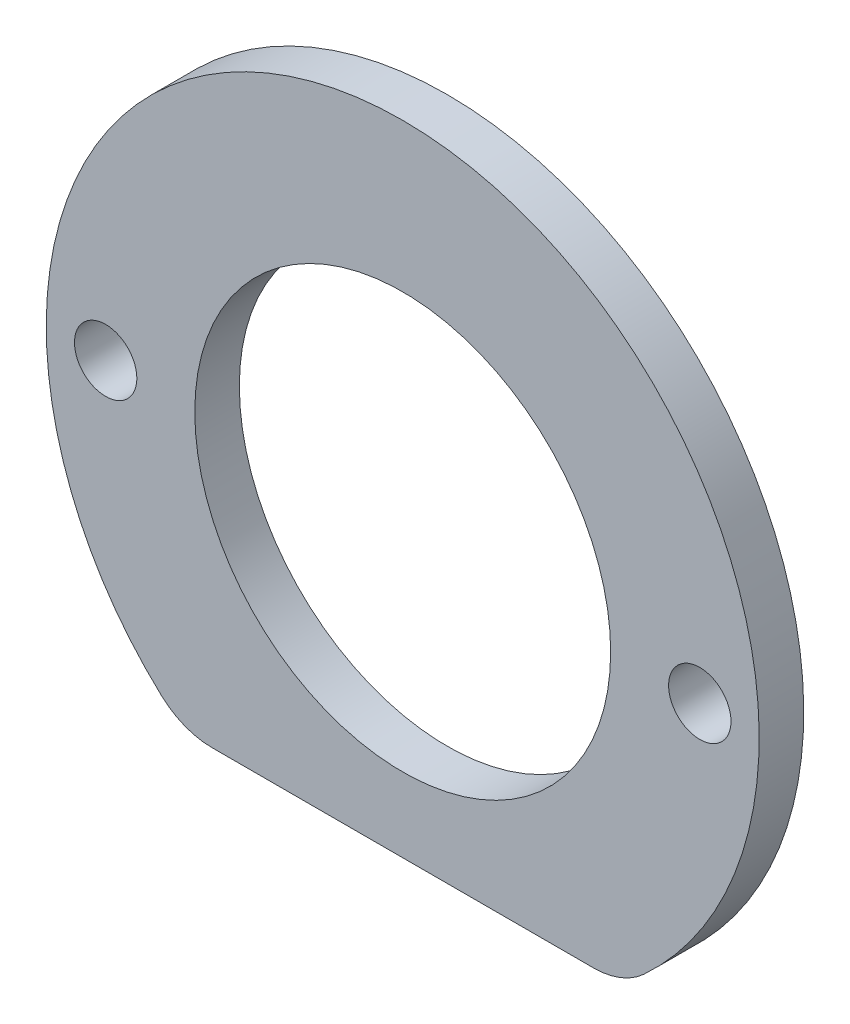
SolidWorks part; units mm, degrees
material "Gerais  - 6061-T6"
ref_plane "Plano frontal" through (0, 0, 0) normal (0, 0, 1) x (1, 0, 0)
ref_plane "Plano superior" through (0, 0, 0) normal (0, 1, 0) x (1, 0, 0)
ref_plane "Plano direito" through (0, 0, 0) normal (1, 0, 0) x (0, 0, -1)
sketch "Esboço1" plane through (0, 0, 0) normal (0, 0, 1) x (1, 0, 0)
  line L0 (-20, 0) -> (20, 0) construction
  line L1 (14.6629, -19) -> (-14.6629, -19)
  line L2 (0, -19) -> (0, -14) construction
  line L4 (0, 0) -> (0, -24) construction
  circle A0 centre (0, 0) radius 14
  circle A1 centre (0, 0) radius 24
  circle A2 centre (-20, 0) radius 2.1
  circle A3 centre (20, 0) radius 2.1
  point P12 (20.7472, -2.4903)
  dimension "D1" = 28
  dimension "D2" = 48
  dimension "D3" = 40
  dimension "D4" = 4.2
  dimension "D5" = 5
extrude "Ressalto-extrusão1" add sketch "Esboço1" along normal blind 3 contours L1 A1 A3 A2 A0
fillet "Filete1" radius 5 2 edges at (14.6629, -19, 1.5) (-14.6629, -19, 1.5)
